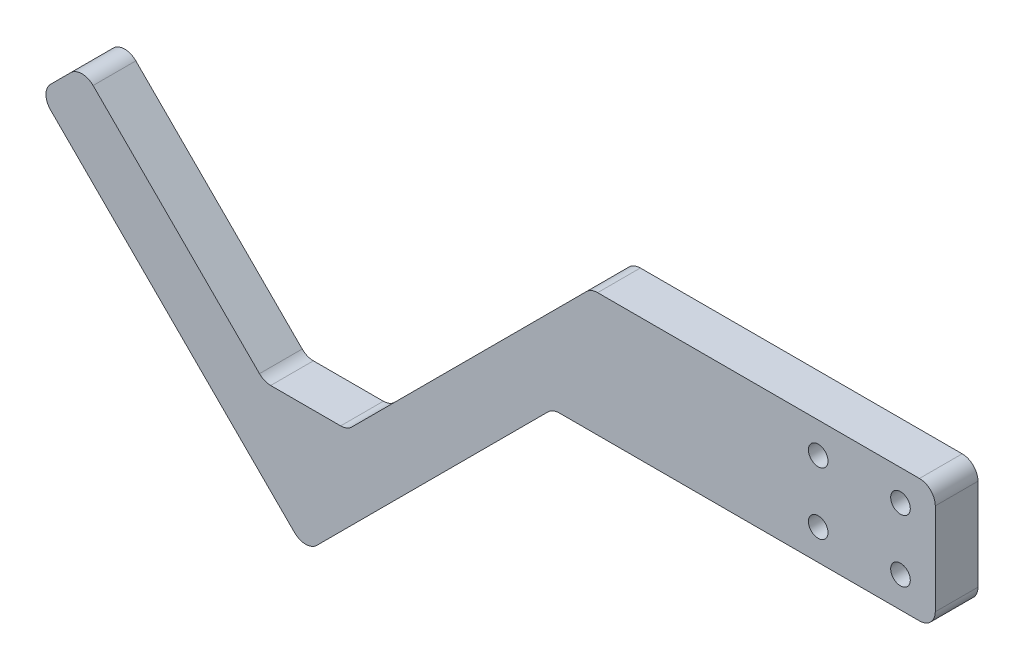
SolidWorks part; units mm, degrees
material "Cast Carbon Steel"
ref_plane "Front Plane" through (0, 0, 0) normal (0, 0, 1) x (1, 0, 0)
ref_plane "Top Plane" through (0, 0, 0) normal (0, 1, 0) x (1, 0, 0)
ref_plane "Right Plane" through (0, 0, 0) normal (1, 0, 0) x (0, 0, -1)
sketch "Sketch1" plane through (0, 0, 0) normal (0, 0, 1) x (1, 0, 0)
  line L0 (0, -1242.5523) -> (0, 60885.0605) construction
  line L1 (-1242.5523, 0) -> (60885.0605, 0) construction
  line L2 (-70.7107, 0) -> (0, -70.7107)
  line L3 (-70.7107, 0) -> (-84.1457, -13.435)
  line L4 (-84.1457, -13.435) -> (0, -97.5807)
  line L5 (0, -97.5807) -> (78.0807, -19.5)
  line L6 (78.0807, -19.5) -> (199, -19.5)
  line L7 (199, -19.5) -> (199, 19.5)
  line L8 (199, 19.5) -> (90.2107, 19.5)
  line L9 (0, -70.7107) -> (90.2107, 19.5)
  line L10 (162, -9.8) -> (188, -9.8) construction
  line L11 (162, -9.8) -> (162, 9.8) construction
  line L12 (162, 9.8) -> (188, 9.8) construction
  line L13 (188, -9.8) -> (188, 9.8) construction
  line L14 (175, 9.8) -> (175, -9.8) construction
  line L15 (162, 0) -> (188, 0) construction
  line L16 (-13.1299, -57.5807) -> (13.1299, -57.5807)
  circle A0 centre (188, 9.8) radius 3.1
  circle A1 centre (162, 9.8) radius 3.1
  circle A2 centre (162, -9.8) radius 3.1
  circle A3 centre (188, -9.8) radius 3.1
  point P14 (175, 0)
  point P26 (199, 0)
  dimension "D2" = 6.2
  dimension "D4" = 26
  dimension "D1" = 100
  dimension "D3" = 19.6
  dimension "D5" = 175
  dimension "D6" = 39
  dimension "D7" = 19
  dimension "D8" = 45
  dimension "D9" = 45
  dimension "D10" = 40
  dimension "D11" = 24
extrude "Boss-Extrude1" add sketch "Sketch1" along normal blind 13.5 contours L16 L2 L9 | L9 L2 L3 L4 L5 L6 L7 L8 A3 A2 A1 A0
fillet "Fillet1" radius 5 9 edges at (13.1299, -57.5807, 6.75) (90.2107, 19.5, 6.75) (199, -19.5, 6.75) (78.0807, -19.5, 6.75) (0, -97.5807, 6.75) (-84.1457, -13.435, 6.75) (-70.7107, 0, 6.75) (-13.1299, -57.5807, 6.75) (199, 19.5, 6.75)
